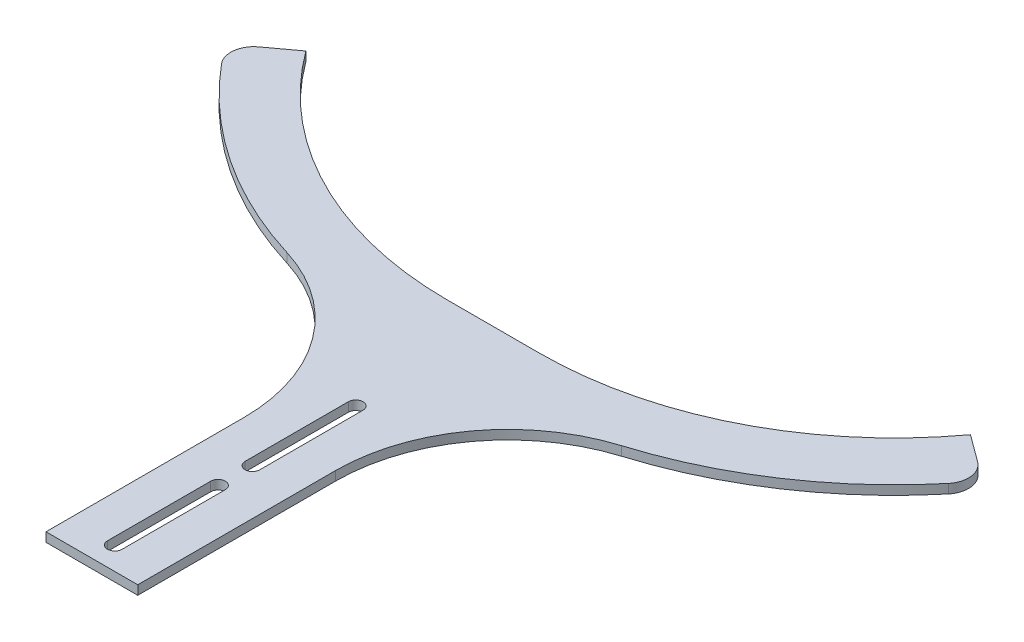
SolidWorks part; units mm, degrees
ref_plane "Front Plane" through (0, 0, 0) normal (0, 0, 1) x (1, 0, 0)
ref_plane "Top Plane" through (0, 0, 0) normal (0, 1, 0) x (1, 0, 0)
ref_plane "Right Plane" through (0, 0, 0) normal (1, 0, 0) x (0, 0, -1)
sketch "Sketch1" plane through (0, 0, 0) normal (0, 1, 0) x (1, 0, 0)
  line L0 (0, 0) -> (0, 94.1227) construction
  line L2 (-20, 11.2788) -> (-20, -75)
  line L3 (-20, -75) -> (20, -75)
  line L4 (20, 11.2788) -> (20, -75)
  line L5 (-20, 75) -> (20, -75) construction
  line L6 (-20, -75) -> (20, 75) construction
  line L7 (-165, 148.3464) -> (-144.8611, 163.1594)
  line L8 (-20, 100) -> (20, 100)
  line L9 (165, 148.3464) -> (144.8611, 163.1594)
  arc A0 (-72.9412, 82.9615) -> (-165, 148.3464) centre (-20, 255) cw
  arc A1 (-20, 100) -> (-144.8611, 163.1594) centre (-20, 255) cw
  arc A2 (72.9412, 82.9615) -> (165, 148.3464) centre (20, 255) ccw
  arc A3 (20, 100) -> (144.8611, 163.1594) centre (20, 255) ccw
  arc A4 (72.9412, 82.9615) -> (20, 11.2788) centre (95, 11.2788) ccw
  arc A5 (-20, 75) -> (-165, 148.3464) centre (-20, 255) cw construction
  arc A6 (-72.9412, 82.9615) -> (-20, 11.2788) centre (-95, 11.2788) cw
  point P0 (0, 0)
  point P4 (0, 100)
  dimension "D4" = 180
  dimension "D6" = 75
  dimension "D1" = 40
  dimension "D2" = 150
  dimension "D5" = 145
  dimension "D3" = 25
extrude "Boss-Extrude1" add sketch "Sketch1" along normal blind 4
fillet "Fillet1" radius 10 2 edges at (165, 2, -148.3464) (-165, 2, -148.3464)
sketch "Sketch2" plane through (0, 4, 0) normal (0, 1, 0) x (1, 0, 0)
  line L0 (0, -75) -> (0, 100) construction
  line L1 (-20, -75) -> (20, -75) construction
  line L2 (-20, 100) -> (20, 100) construction
  line L3 (0, 40) -> (0, -5) construction
  line L4 (3.2, 40) -> (3.2, -5)
  line L5 (-3.2, 40) -> (-3.2, -5)
  line L6 (0, -20) -> (0, -65) construction
  line L7 (3.2, -20) -> (3.2, -65)
  line L8 (-3.2, -20) -> (-3.2, -65)
  arc A0 (3.2, 40) -> (-3.2, 40) centre (0, 40) ccw
  arc A1 (-3.2, -5) -> (3.2, -5) centre (0, -5) ccw
  arc A2 (3.2, -20) -> (-3.2, -20) centre (0, -20) ccw
  arc A3 (-3.2, -65) -> (3.2, -65) centre (0, -65) ccw
  point P8 (0, 17.5)
  point P13 (0, -42.5)
  dimension "D1" = 6.4
  dimension "D2" = 45
  dimension "D3" = 6.4
  dimension "D4" = 45
  dimension "D5" = 60
  dimension "D6" = 10
extrude "Cut-Extrude1" cut sketch "Sketch2" against normal blind 10
